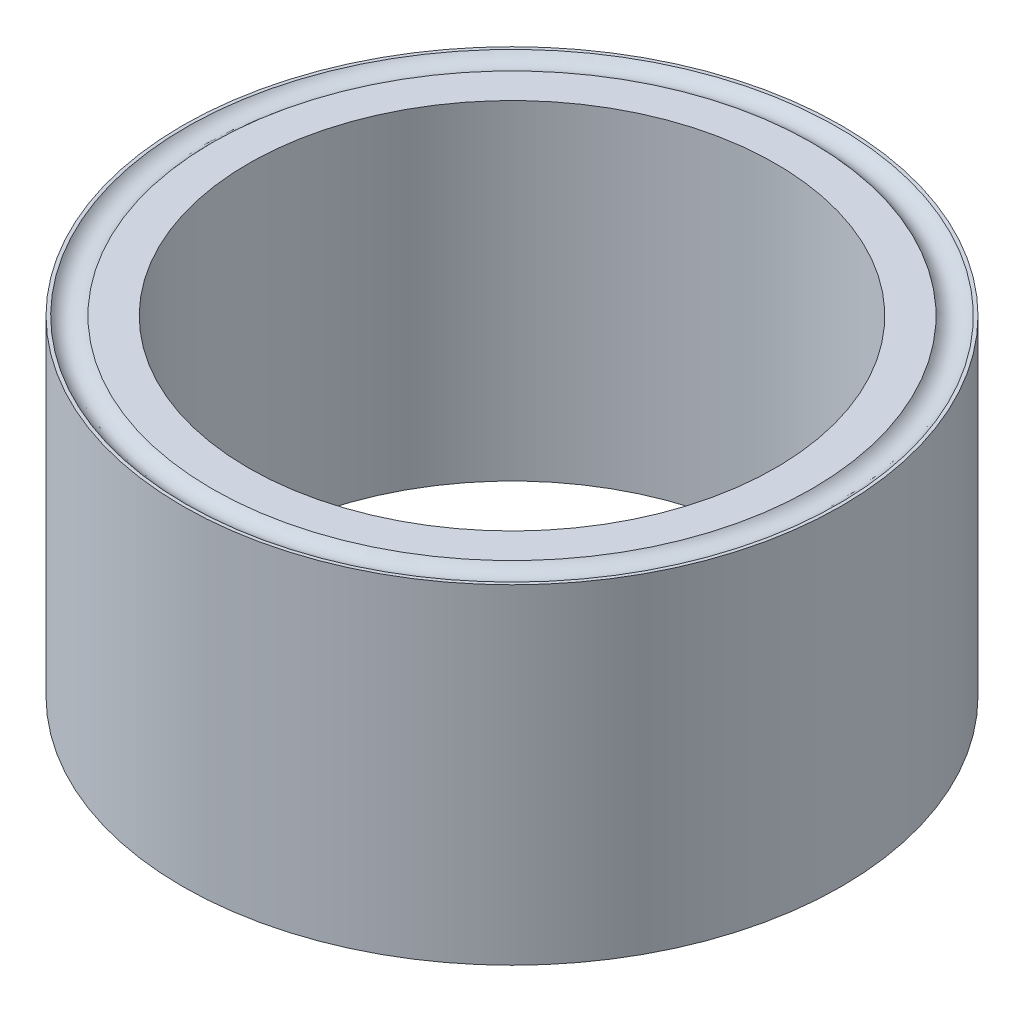
SolidWorks part; units mm, degrees
ref_plane "Front Plane" through (0, 0, 0) normal (0, 0, 1) x (1, 0, 0)
ref_plane "Top Plane" through (0, 0, 0) normal (0, 1, 0) x (1, 0, 0)
ref_plane "Right Plane" through (0, 0, 0) normal (1, 0, 0) x (0, 0, -1)
sketch "Sketch1" plane through (0, 0, 0) normal (0, 1, 0) x (1, 0, 0)
  circle A0 centre (0, 0) radius 25
  circle A1 centre (0, 0) radius 20
  dimension "D1" = 5
  dimension "D2" = 50
extrude "Boss-Extrude1" add sketch "Sketch1" along normal blind 25
sketch "Sketch2" plane through (0, 0, 0) normal (0, 0, 1) x (1, 0, 0)
  line L0 (0, 26.2194) -> (0, 0) construction
  line L1 (-24.75, 25) -> (-22.75, 25)
  line L6 (25, 25) -> (-25, 25) construction
  arc A1 (-24.75, 25) -> (-22.75, 25) centre (-23.75, 25.75) ccw
  point P9 (-23.75, 25)
  dimension "D2" = 1.25
  dimension "D3" = 23.75
  dimension "D1" = 2
revolve "Cut-Revolve1" cut sketch "Sketch2" angle 360 about L0
